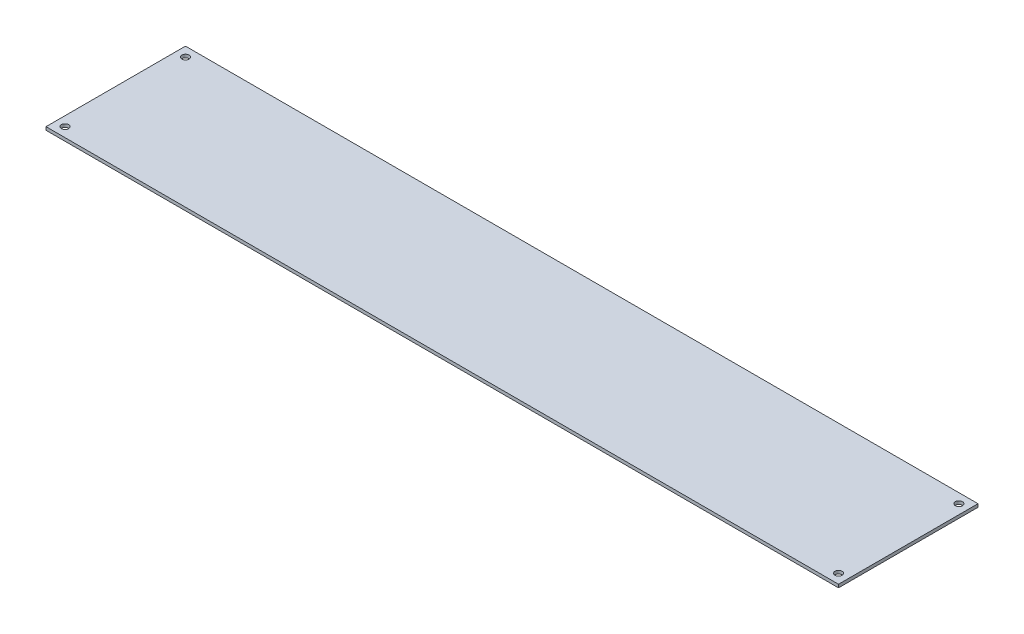
SolidWorks part; units mm, degrees
ref_plane "Front Plane" through (0, 0, 0) normal (0, 0, 1) x (1, 0, 0)
ref_plane "Top Plane" through (0, 0, 0) normal (0, 1, 0) x (1, 0, 0)
ref_plane "Right Plane" through (0, 0, 0) normal (1, 0, 0) x (0, 0, -1)
sketch "Sketch1" plane through (0, 0, 0) normal (0, 1, 0) x (1, 0, 0)
  line L1 (0, 0) -> (500, 0)
  line L2 (0, 0) -> (0, 88)
  line L3 (0, 88) -> (500, 88)
  line L4 (500, 0) -> (500, 88)
  dimension "D1" = 500
  dimension "D2" = 88
extrude "Boss-Extrude1" add sketch "Sketch1" along normal blind 2
hole_wizard "M4 Clearance Hole1" positions "Sketch2" profile "Sketch3" hole size "M4" standard "DIN" end condition up to next
sketch "Sketch2" plane through (0, 2, 0) normal (0, 1, 0) x (1, 0, 0)
  line L0 (500, 88) -> (0, 88) construction
  line L1 (0, 88) -> (0, 0) construction
  line L2 (0, 0) -> (500, 0) construction
  line L3 (500, 0) -> (500, 88) construction
  point P0 (6, 82)
  point P2 (6, 6)
  point P4 (494, 6)
  point P6 (494, 82)
  dimension "D1" = 6
  dimension "D2" = 6
  dimension "D3" = 6
  dimension "D4" = 6
sketch "Sketch3" plane through (6, 2, -82) normal (1, 0, 0) x (0, 0, 1)
  line L0 (0, 0) -> (0, 2)
  line L1 (0, 2) -> (2.25, 2)
  line L2 (2.25, 2) -> (2.25, 0)
  line L5 (2.25, 0) -> (0, 0)
  line L11 (0, -6.35) -> (0, 107.95) construction
  dimension "Thru Hole Dia." = 4.5
  dimension "Thru Hole Depth" = 2
sketch "Sketch4" plane through (0, 2, 0) normal (0, 1, 0) x (1, 0, 0)
  line L0 (500, 0) -> (500, 88) construction
  line L1 (0, 0) -> (500, 0) construction
  line L3 (369.3868, 83) -> (367.9434, 85.5)
  line L4 (367.9434, 85.5) -> (365.0566, 85.5)
  line L5 (365.0566, 85.5) -> (363.6132, 83)
  line L6 (363.6132, 83) -> (365.0566, 80.5)
  line L7 (365.0566, 80.5) -> (367.9434, 80.5)
  line L8 (367.9434, 80.5) -> (369.3868, 83)
  line L9 (379.3868, 83) -> (377.9434, 85.5)
  line L10 (377.9434, 85.5) -> (375.0566, 85.5)
  line L11 (375.0566, 85.5) -> (373.6132, 83)
  line L12 (373.6132, 83) -> (375.0566, 80.5)
  line L13 (375.0566, 80.5) -> (377.9434, 80.5)
  line L14 (377.9434, 80.5) -> (379.3868, 83)
  line L15 (389.3868, 83) -> (387.9434, 85.5)
  line L16 (387.9434, 85.5) -> (385.0566, 85.5)
  line L17 (385.0566, 85.5) -> (383.6132, 83)
  line L18 (383.6132, 83) -> (385.0566, 80.5)
  line L19 (385.0566, 80.5) -> (387.9434, 80.5)
  line L20 (387.9434, 80.5) -> (389.3868, 83)
  line L21 (399.3868, 83) -> (397.9434, 85.5)
  line L22 (397.9434, 85.5) -> (395.0566, 85.5)
  line L23 (395.0566, 85.5) -> (393.6132, 83)
  line L24 (393.6132, 83) -> (395.0566, 80.5)
  line L25 (395.0566, 80.5) -> (397.9434, 80.5)
  line L26 (397.9434, 80.5) -> (399.3868, 83)
  line L27 (409.3868, 83) -> (407.9434, 85.5)
  line L28 (407.9434, 85.5) -> (405.0566, 85.5)
  line L29 (405.0566, 85.5) -> (403.6132, 83)
  line L30 (403.6132, 83) -> (405.0566, 80.5)
  line L31 (405.0566, 80.5) -> (407.9434, 80.5)
  line L32 (407.9434, 80.5) -> (409.3868, 83)
  line L33 (419.3868, 83) -> (417.9434, 85.5)
  line L34 (417.9434, 85.5) -> (415.0566, 85.5)
  line L35 (415.0566, 85.5) -> (413.6132, 83)
  line L36 (413.6132, 83) -> (415.0566, 80.5)
  line L37 (415.0566, 80.5) -> (417.9434, 80.5)
  line L38 (417.9434, 80.5) -> (419.3868, 83)
  line L39 (429.3868, 83) -> (427.9434, 85.5)
  line L40 (427.9434, 85.5) -> (425.0566, 85.5)
  line L41 (425.0566, 85.5) -> (423.6132, 83)
  line L42 (423.6132, 83) -> (425.0566, 80.5)
  line L43 (425.0566, 80.5) -> (427.9434, 80.5)
  line L44 (427.9434, 80.5) -> (429.3868, 83)
  line L45 (439.3868, 83) -> (437.9434, 85.5)
  line L46 (437.9434, 85.5) -> (435.0566, 85.5)
  line L47 (435.0566, 85.5) -> (433.6132, 83)
  line L48 (433.6132, 83) -> (435.0566, 80.5)
  line L49 (435.0566, 80.5) -> (437.9434, 80.5)
  line L50 (437.9434, 80.5) -> (439.3868, 83)
  line L51 (449.3868, 83) -> (447.9434, 85.5)
  line L52 (447.9434, 85.5) -> (445.0566, 85.5)
  line L53 (445.0566, 85.5) -> (443.6132, 83)
  line L54 (443.6132, 83) -> (445.0566, 80.5)
  line L55 (445.0566, 80.5) -> (447.9434, 80.5)
  line L56 (447.9434, 80.5) -> (449.3868, 83)
  line L57 (459.3868, 83) -> (457.9434, 85.5)
  line L58 (457.9434, 85.5) -> (455.0566, 85.5)
  line L59 (455.0566, 85.5) -> (453.6132, 83)
  line L60 (453.6132, 83) -> (455.0566, 80.5)
  line L61 (455.0566, 80.5) -> (457.9434, 80.5)
  line L62 (457.9434, 80.5) -> (459.3868, 83)
  line L63 (469.3868, 83) -> (467.9434, 85.5)
  line L64 (467.9434, 85.5) -> (465.0566, 85.5)
  line L65 (465.0566, 85.5) -> (463.6132, 83)
  line L66 (463.6132, 83) -> (465.0566, 80.5)
  line L67 (465.0566, 80.5) -> (467.9434, 80.5)
  line L68 (467.9434, 80.5) -> (469.3868, 83)
  line L69 (379.3868, 73) -> (377.9434, 75.5)
  line L70 (377.9434, 75.5) -> (375.0566, 75.5)
  line L71 (375.0566, 75.5) -> (373.6132, 73)
  line L72 (373.6132, 73) -> (375.0566, 70.5)
  line L73 (375.0566, 70.5) -> (377.9434, 70.5)
  line L74 (377.9434, 70.5) -> (379.3868, 73)
  line L75 (389.3868, 73) -> (387.9434, 75.5)
  line L76 (387.9434, 75.5) -> (385.0566, 75.5)
  line L77 (385.0566, 75.5) -> (383.6132, 73)
  line L78 (383.6132, 73) -> (385.0566, 70.5)
  line L79 (385.0566, 70.5) -> (387.9434, 70.5)
  line L80 (387.9434, 70.5) -> (389.3868, 73)
  line L81 (399.3868, 73) -> (397.9434, 75.5)
  line L82 (397.9434, 75.5) -> (395.0566, 75.5)
  line L83 (395.0566, 75.5) -> (393.6132, 73)
  line L84 (393.6132, 73) -> (395.0566, 70.5)
  line L85 (395.0566, 70.5) -> (397.9434, 70.5)
  line L86 (397.9434, 70.5) -> (399.3868, 73)
  line L87 (409.3868, 73) -> (407.9434, 75.5)
  line L88 (407.9434, 75.5) -> (405.0566, 75.5)
  line L89 (405.0566, 75.5) -> (403.6132, 73)
  line L90 (403.6132, 73) -> (405.0566, 70.5)
  line L91 (405.0566, 70.5) -> (407.9434, 70.5)
  line L92 (407.9434, 70.5) -> (409.3868, 73)
  line L93 (419.3868, 73) -> (417.9434, 75.5)
  line L94 (417.9434, 75.5) -> (415.0566, 75.5)
  line L95 (415.0566, 75.5) -> (413.6132, 73)
  line L96 (413.6132, 73) -> (415.0566, 70.5)
  line L97 (415.0566, 70.5) -> (417.9434, 70.5)
  line L98 (417.9434, 70.5) -> (419.3868, 73)
  line L99 (429.3868, 73) -> (427.9434, 75.5)
  line L100 (427.9434, 75.5) -> (425.0566, 75.5)
  line L101 (425.0566, 75.5) -> (423.6132, 73)
  line L102 (423.6132, 73) -> (425.0566, 70.5)
  line L103 (425.0566, 70.5) -> (427.9434, 70.5)
  line L104 (427.9434, 70.5) -> (429.3868, 73)
  line L105 (439.3868, 73) -> (437.9434, 75.5)
  line L106 (437.9434, 75.5) -> (435.0566, 75.5)
  line L107 (435.0566, 75.5) -> (433.6132, 73)
  line L108 (433.6132, 73) -> (435.0566, 70.5)
  line L109 (435.0566, 70.5) -> (437.9434, 70.5)
  line L110 (437.9434, 70.5) -> (439.3868, 73)
  line L111 (449.3868, 73) -> (447.9434, 75.5)
  line L112 (447.9434, 75.5) -> (445.0566, 75.5)
  line L113 (445.0566, 75.5) -> (443.6132, 73)
  line L114 (443.6132, 73) -> (445.0566, 70.5)
  line L115 (445.0566, 70.5) -> (447.9434, 70.5)
  line L116 (447.9434, 70.5) -> (449.3868, 73)
  line L117 (459.3868, 73) -> (457.9434, 75.5)
  line L118 (457.9434, 75.5) -> (455.0566, 75.5)
  line L119 (455.0566, 75.5) -> (453.6132, 73)
  line L120 (453.6132, 73) -> (455.0566, 70.5)
  line L121 (455.0566, 70.5) -> (457.9434, 70.5)
  line L122 (457.9434, 70.5) -> (459.3868, 73)
  line L135 (389.3868, 63) -> (387.9434, 65.5)
  line L136 (387.9434, 65.5) -> (385.0566, 65.5)
  line L137 (385.0566, 65.5) -> (383.6132, 63)
  line L138 (383.6132, 63) -> (385.0566, 60.5)
  line L139 (385.0566, 60.5) -> (387.9434, 60.5)
  line L140 (387.9434, 60.5) -> (389.3868, 63)
  line L141 (399.3868, 63) -> (397.9434, 65.5)
  line L142 (397.9434, 65.5) -> (395.0566, 65.5)
  line L143 (395.0566, 65.5) -> (393.6132, 63)
  line L144 (393.6132, 63) -> (395.0566, 60.5)
  line L145 (395.0566, 60.5) -> (397.9434, 60.5)
  line L146 (397.9434, 60.5) -> (399.3868, 63)
  line L147 (409.3868, 63) -> (407.9434, 65.5)
  line L148 (407.9434, 65.5) -> (405.0566, 65.5)
  line L149 (405.0566, 65.5) -> (403.6132, 63)
  line L150 (403.6132, 63) -> (405.0566, 60.5)
  line L151 (405.0566, 60.5) -> (407.9434, 60.5)
  line L152 (407.9434, 60.5) -> (409.3868, 63)
  line L153 (419.3868, 63) -> (417.9434, 65.5)
  line L154 (417.9434, 65.5) -> (415.0566, 65.5)
  line L155 (415.0566, 65.5) -> (413.6132, 63)
  line L156 (413.6132, 63) -> (415.0566, 60.5)
  line L157 (415.0566, 60.5) -> (417.9434, 60.5)
  line L158 (417.9434, 60.5) -> (419.3868, 63)
  line L159 (429.3868, 63) -> (427.9434, 65.5)
  line L160 (427.9434, 65.5) -> (425.0566, 65.5)
  line L161 (425.0566, 65.5) -> (423.6132, 63)
  line L162 (423.6132, 63) -> (425.0566, 60.5)
  line L163 (425.0566, 60.5) -> (427.9434, 60.5)
  line L164 (427.9434, 60.5) -> (429.3868, 63)
  line L165 (439.3868, 63) -> (437.9434, 65.5)
  line L166 (437.9434, 65.5) -> (435.0566, 65.5)
  line L167 (435.0566, 65.5) -> (433.6132, 63)
  line L168 (433.6132, 63) -> (435.0566, 60.5)
  line L169 (435.0566, 60.5) -> (437.9434, 60.5)
  line L170 (437.9434, 60.5) -> (439.3868, 63)
  line L171 (449.3868, 63) -> (447.9434, 65.5)
  line L172 (447.9434, 65.5) -> (445.0566, 65.5)
  line L173 (445.0566, 65.5) -> (443.6132, 63)
  line L174 (443.6132, 63) -> (445.0566, 60.5)
  line L175 (445.0566, 60.5) -> (447.9434, 60.5)
  line L176 (447.9434, 60.5) -> (449.3868, 63)
  line L207 (409.3868, 53) -> (407.9434, 55.5)
  line L208 (407.9434, 55.5) -> (405.0566, 55.5)
  line L209 (405.0566, 55.5) -> (403.6132, 53)
  line L210 (403.6132, 53) -> (405.0566, 50.5)
  line L211 (405.0566, 50.5) -> (407.9434, 50.5)
  line L212 (407.9434, 50.5) -> (409.3868, 53)
  line L213 (419.3868, 53) -> (417.9434, 55.5)
  line L214 (417.9434, 55.5) -> (415.0566, 55.5)
  line L215 (415.0566, 55.5) -> (413.6132, 53)
  line L216 (413.6132, 53) -> (415.0566, 50.5)
  line L217 (415.0566, 50.5) -> (417.9434, 50.5)
  line L218 (417.9434, 50.5) -> (419.3868, 53)
  line L219 (429.3868, 53) -> (427.9434, 55.5)
  line L220 (427.9434, 55.5) -> (425.0566, 55.5)
  line L221 (425.0566, 55.5) -> (423.6132, 53)
  line L222 (423.6132, 53) -> (425.0566, 50.5)
  line L223 (425.0566, 50.5) -> (427.9434, 50.5)
  line L224 (427.9434, 50.5) -> (429.3868, 53)
  line L267 (369.3868, 73) -> (367.9434, 75.5) [skipped]
  line L268 (367.9434, 75.5) -> (365.0566, 75.5) [skipped]
  line L269 (365.0566, 75.5) -> (363.6132, 73) [skipped]
  line L270 (363.6132, 73) -> (365.0566, 70.5) [skipped]
  line L271 (365.0566, 70.5) -> (367.9434, 70.5) [skipped]
  line L272 (367.9434, 70.5) -> (369.3868, 73) [skipped]
  line L273 (369.3868, 63) -> (367.9434, 65.5) [skipped]
  line L274 (367.9434, 65.5) -> (365.0566, 65.5) [skipped]
  line L275 (365.0566, 65.5) -> (363.6132, 63) [skipped]
  line L276 (363.6132, 63) -> (365.0566, 60.5) [skipped]
  line L277 (365.0566, 60.5) -> (367.9434, 60.5) [skipped]
  line L278 (367.9434, 60.5) -> (369.3868, 63) [skipped]
  line L279 (369.3868, 53) -> (367.9434, 55.5) [skipped]
  line L280 (367.9434, 55.5) -> (365.0566, 55.5) [skipped]
  line L281 (365.0566, 55.5) -> (363.6132, 53) [skipped]
  line L282 (363.6132, 53) -> (365.0566, 50.5) [skipped]
  line L283 (365.0566, 50.5) -> (367.9434, 50.5) [skipped]
  line L284 (367.9434, 50.5) -> (369.3868, 53) [skipped]
  line L285 (379.3868, 53) -> (377.9434, 55.5) [skipped]
  line L286 (377.9434, 55.5) -> (375.0566, 55.5) [skipped]
  line L287 (375.0566, 55.5) -> (373.6132, 53) [skipped]
  line L288 (373.6132, 53) -> (375.0566, 50.5) [skipped]
  line L289 (375.0566, 50.5) -> (377.9434, 50.5) [skipped]
  line L290 (377.9434, 50.5) -> (379.3868, 53) [skipped]
  line L291 (379.3868, 63) -> (377.9434, 65.5) [skipped]
  line L292 (377.9434, 65.5) -> (375.0566, 65.5) [skipped]
  line L293 (375.0566, 65.5) -> (373.6132, 63) [skipped]
  line L294 (373.6132, 63) -> (375.0566, 60.5) [skipped]
  line L295 (375.0566, 60.5) -> (377.9434, 60.5) [skipped]
  line L296 (377.9434, 60.5) -> (379.3868, 63) [skipped]
  line L297 (389.3868, 53) -> (387.9434, 55.5) [skipped]
  line L298 (387.9434, 55.5) -> (385.0566, 55.5) [skipped]
  line L299 (385.0566, 55.5) -> (383.6132, 53) [skipped]
  line L300 (383.6132, 53) -> (385.0566, 50.5) [skipped]
  line L301 (385.0566, 50.5) -> (387.9434, 50.5) [skipped]
  line L302 (387.9434, 50.5) -> (389.3868, 53) [skipped]
  line L303 (399.3868, 53) -> (397.9434, 55.5) [skipped]
  line L304 (397.9434, 55.5) -> (395.0566, 55.5) [skipped]
  line L305 (395.0566, 55.5) -> (393.6132, 53) [skipped]
  line L306 (393.6132, 53) -> (395.0566, 50.5) [skipped]
  line L307 (395.0566, 50.5) -> (397.9434, 50.5) [skipped]
  line L308 (397.9434, 50.5) -> (399.3868, 53) [skipped]
  line L309 (439.3868, 53) -> (437.9434, 55.5) [skipped]
  line L310 (437.9434, 55.5) -> (435.0566, 55.5) [skipped]
  line L311 (435.0566, 55.5) -> (433.6132, 53) [skipped]
  line L312 (433.6132, 53) -> (435.0566, 50.5) [skipped]
  line L313 (435.0566, 50.5) -> (437.9434, 50.5) [skipped]
  line L314 (437.9434, 50.5) -> (439.3868, 53) [skipped]
  line L315 (449.3868, 53) -> (447.9434, 55.5) [skipped]
  line L316 (447.9434, 55.5) -> (445.0566, 55.5) [skipped]
  line L317 (445.0566, 55.5) -> (443.6132, 53) [skipped]
  line L318 (443.6132, 53) -> (445.0566, 50.5) [skipped]
  line L319 (445.0566, 50.5) -> (447.9434, 50.5) [skipped]
  line L320 (447.9434, 50.5) -> (449.3868, 53) [skipped]
  line L321 (459.3868, 63) -> (457.9434, 65.5) [skipped]
  line L322 (457.9434, 65.5) -> (455.0566, 65.5) [skipped]
  line L323 (455.0566, 65.5) -> (453.6132, 63) [skipped]
  line L324 (453.6132, 63) -> (455.0566, 60.5) [skipped]
  line L325 (455.0566, 60.5) -> (457.9434, 60.5) [skipped]
  line L326 (457.9434, 60.5) -> (459.3868, 63) [skipped]
  line L327 (459.3868, 53) -> (457.9434, 55.5) [skipped]
  line L328 (457.9434, 55.5) -> (455.0566, 55.5) [skipped]
  line L329 (455.0566, 55.5) -> (453.6132, 53) [skipped]
  line L330 (453.6132, 53) -> (455.0566, 50.5) [skipped]
  line L331 (455.0566, 50.5) -> (457.9434, 50.5) [skipped]
  line L332 (457.9434, 50.5) -> (459.3868, 53) [skipped]
  line L333 (469.3868, 53) -> (467.9434, 55.5) [skipped]
  line L334 (467.9434, 55.5) -> (465.0566, 55.5) [skipped]
  line L335 (465.0566, 55.5) -> (463.6132, 53) [skipped]
  line L336 (463.6132, 53) -> (465.0566, 50.5) [skipped]
  line L337 (465.0566, 50.5) -> (467.9434, 50.5) [skipped]
  line L338 (467.9434, 50.5) -> (469.3868, 53) [skipped]
  line L339 (469.3868, 63) -> (467.9434, 65.5) [skipped]
  line L340 (467.9434, 65.5) -> (465.0566, 65.5) [skipped]
  line L341 (465.0566, 65.5) -> (463.6132, 63) [skipped]
  line L342 (463.6132, 63) -> (465.0566, 60.5) [skipped]
  line L343 (465.0566, 60.5) -> (467.9434, 60.5) [skipped]
  line L344 (467.9434, 60.5) -> (469.3868, 63) [skipped]
  line L345 (469.3868, 73) -> (467.9434, 75.5) [skipped]
  line L346 (467.9434, 75.5) -> (465.0566, 75.5) [skipped]
  line L347 (465.0566, 75.5) -> (463.6132, 73) [skipped]
  line L348 (463.6132, 73) -> (465.0566, 70.5) [skipped]
  line L349 (465.0566, 70.5) -> (467.9434, 70.5) [skipped]
  line L350 (467.9434, 70.5) -> (469.3868, 73) [skipped]
  line L351 (500, 88) -> (0, 88) construction
  circle A0 centre (416.5, 113) radius 66 construction
  circle A1 centre (366.5, 83) radius 2.5 construction
  dimension "D1" = 132
  dimension "D2" = 83.5
  dimension "D3" = 113
  dimension "D4" = 5
  dimension "D5" = 50
  dimension "D6" = 5
  dimension "D9" = 10
  dimension "D10" = 10
  dimension "D7" = 11
  dimension "D8" = 4
extrude "Cut-Extrude1" [suppressed] cut sketch "Sketch4" against normal up to next
sketch "Sketch5" [suppressed] plane through (0, 2, 0) normal (0, 1, 0) x (1, 0, 0)
  line L217 (384.3868, 78) -> (382.9434, 80.5)
  line L218 (374.3868, 78) -> (372.9434, 80.5)
  line L219 (372.9434, 80.5) -> (370.0566, 80.5)
  line L220 (370.0566, 80.5) -> (368.6132, 78)
  line L221 (368.6132, 78) -> (370.0566, 75.5)
  line L222 (370.0566, 75.5) -> (372.9434, 75.5)
  line L223 (372.9434, 75.5) -> (374.3868, 78)
  line L224 (382.9434, 80.5) -> (380.0566, 80.5)
  line L225 (380.0566, 80.5) -> (378.6132, 78)
  line L226 (378.6132, 78) -> (380.0566, 75.5)
  line L227 (380.0566, 75.5) -> (382.9434, 75.5)
  line L228 (382.9434, 75.5) -> (384.3868, 78)
  line L229 (394.3868, 78) -> (392.9434, 80.5)
  line L230 (392.9434, 80.5) -> (390.0566, 80.5)
  line L231 (390.0566, 80.5) -> (388.6132, 78)
  line L232 (388.6132, 78) -> (390.0566, 75.5)
  line L233 (390.0566, 75.5) -> (392.9434, 75.5)
  line L234 (392.9434, 75.5) -> (394.3868, 78)
  line L235 (404.3868, 78) -> (402.9434, 80.5)
  line L236 (402.9434, 80.5) -> (400.0566, 80.5)
  line L237 (400.0566, 80.5) -> (398.6132, 78)
  line L238 (398.6132, 78) -> (400.0566, 75.5)
  line L239 (400.0566, 75.5) -> (402.9434, 75.5)
  line L240 (402.9434, 75.5) -> (404.3868, 78)
  line L241 (414.3868, 78) -> (412.9434, 80.5)
  line L242 (412.9434, 80.5) -> (410.0566, 80.5)
  line L243 (410.0566, 80.5) -> (408.6132, 78)
  line L244 (408.6132, 78) -> (410.0566, 75.5)
  line L245 (410.0566, 75.5) -> (412.9434, 75.5)
  line L246 (412.9434, 75.5) -> (414.3868, 78)
  line L247 (424.3868, 78) -> (422.9434, 80.5)
  line L248 (422.9434, 80.5) -> (420.0566, 80.5)
  line L249 (420.0566, 80.5) -> (418.6132, 78)
  line L250 (418.6132, 78) -> (420.0566, 75.5)
  line L251 (420.0566, 75.5) -> (422.9434, 75.5)
  line L252 (422.9434, 75.5) -> (424.3868, 78)
  line L253 (434.3868, 78) -> (432.9434, 80.5)
  line L254 (432.9434, 80.5) -> (430.0566, 80.5)
  line L255 (430.0566, 80.5) -> (428.6132, 78)
  line L256 (428.6132, 78) -> (430.0566, 75.5)
  line L257 (430.0566, 75.5) -> (432.9434, 75.5)
  line L258 (432.9434, 75.5) -> (434.3868, 78)
  line L259 (444.3868, 78) -> (442.9434, 80.5)
  line L260 (442.9434, 80.5) -> (440.0566, 80.5)
  line L261 (440.0566, 80.5) -> (438.6132, 78)
  line L262 (438.6132, 78) -> (440.0566, 75.5)
  line L263 (440.0566, 75.5) -> (442.9434, 75.5)
  line L264 (442.9434, 75.5) -> (444.3868, 78)
  line L265 (454.3868, 78) -> (452.9434, 80.5)
  line L266 (452.9434, 80.5) -> (450.0566, 80.5)
  line L267 (450.0566, 80.5) -> (448.6132, 78)
  line L268 (448.6132, 78) -> (450.0566, 75.5)
  line L269 (450.0566, 75.5) -> (452.9434, 75.5)
  line L270 (452.9434, 75.5) -> (454.3868, 78)
  line L271 (464.3868, 78) -> (462.9434, 80.5)
  line L272 (462.9434, 80.5) -> (460.0566, 80.5)
  line L273 (460.0566, 80.5) -> (458.6132, 78)
  line L274 (458.6132, 78) -> (460.0566, 75.5)
  line L275 (460.0566, 75.5) -> (462.9434, 75.5)
  line L276 (462.9434, 75.5) -> (464.3868, 78)
  line L277 (384.3868, 68) -> (382.9434, 70.5)
  line L278 (382.9434, 70.5) -> (380.0566, 70.5)
  line L279 (380.0566, 70.5) -> (378.6132, 68)
  line L280 (378.6132, 68) -> (380.0566, 65.5)
  line L281 (380.0566, 65.5) -> (382.9434, 65.5)
  line L282 (382.9434, 65.5) -> (384.3868, 68)
  line L283 (394.3868, 68) -> (392.9434, 70.5)
  line L284 (392.9434, 70.5) -> (390.0566, 70.5)
  line L285 (390.0566, 70.5) -> (388.6132, 68)
  line L286 (388.6132, 68) -> (390.0566, 65.5)
  line L287 (390.0566, 65.5) -> (392.9434, 65.5)
  line L288 (392.9434, 65.5) -> (394.3868, 68)
  line L289 (404.3868, 68) -> (402.9434, 70.5)
  line L290 (402.9434, 70.5) -> (400.0566, 70.5)
  line L291 (400.0566, 70.5) -> (398.6132, 68)
  line L292 (398.6132, 68) -> (400.0566, 65.5)
  line L293 (400.0566, 65.5) -> (402.9434, 65.5)
  line L294 (402.9434, 65.5) -> (404.3868, 68)
  line L295 (414.3868, 68) -> (412.9434, 70.5)
  line L296 (412.9434, 70.5) -> (410.0566, 70.5)
  line L297 (410.0566, 70.5) -> (408.6132, 68)
  line L298 (408.6132, 68) -> (410.0566, 65.5)
  line L299 (410.0566, 65.5) -> (412.9434, 65.5)
  line L300 (412.9434, 65.5) -> (414.3868, 68)
  line L301 (424.3868, 68) -> (422.9434, 70.5)
  line L302 (422.9434, 70.5) -> (420.0566, 70.5)
  line L303 (420.0566, 70.5) -> (418.6132, 68)
  line L304 (418.6132, 68) -> (420.0566, 65.5)
  line L305 (420.0566, 65.5) -> (422.9434, 65.5)
  line L306 (422.9434, 65.5) -> (424.3868, 68)
  line L307 (434.3868, 68) -> (432.9434, 70.5)
  line L308 (432.9434, 70.5) -> (430.0566, 70.5)
  line L309 (430.0566, 70.5) -> (428.6132, 68)
  line L310 (428.6132, 68) -> (430.0566, 65.5)
  line L311 (430.0566, 65.5) -> (432.9434, 65.5)
  line L312 (432.9434, 65.5) -> (434.3868, 68)
  line L313 (444.3868, 68) -> (442.9434, 70.5)
  line L314 (442.9434, 70.5) -> (440.0566, 70.5)
  line L315 (440.0566, 70.5) -> (438.6132, 68)
  line L316 (438.6132, 68) -> (440.0566, 65.5)
  line L317 (440.0566, 65.5) -> (442.9434, 65.5)
  line L318 (442.9434, 65.5) -> (444.3868, 68)
  line L319 (454.3868, 68) -> (452.9434, 70.5)
  line L320 (452.9434, 70.5) -> (450.0566, 70.5)
  line L321 (450.0566, 70.5) -> (448.6132, 68)
  line L322 (448.6132, 68) -> (450.0566, 65.5)
  line L323 (450.0566, 65.5) -> (452.9434, 65.5)
  line L324 (452.9434, 65.5) -> (454.3868, 68)
  line L325 (464.3868, 68) -> (462.9434, 70.5)
  line L326 (462.9434, 70.5) -> (460.0566, 70.5)
  line L327 (460.0566, 70.5) -> (458.6132, 68)
  line L328 (458.6132, 68) -> (460.0566, 65.5)
  line L329 (460.0566, 65.5) -> (462.9434, 65.5)
  line L330 (462.9434, 65.5) -> (464.3868, 68)
  line L337 (394.3868, 58) -> (392.9434, 60.5)
  line L338 (392.9434, 60.5) -> (390.0566, 60.5)
  line L339 (390.0566, 60.5) -> (388.6132, 58)
  line L340 (388.6132, 58) -> (390.0566, 55.5)
  line L341 (390.0566, 55.5) -> (392.9434, 55.5)
  line L342 (392.9434, 55.5) -> (394.3868, 58)
  line L343 (404.3868, 58) -> (402.9434, 60.5)
  line L344 (402.9434, 60.5) -> (400.0566, 60.5)
  line L345 (400.0566, 60.5) -> (398.6132, 58)
  line L346 (398.6132, 58) -> (400.0566, 55.5)
  line L347 (400.0566, 55.5) -> (402.9434, 55.5)
  line L348 (402.9434, 55.5) -> (404.3868, 58)
  line L349 (414.3868, 58) -> (412.9434, 60.5)
  line L350 (412.9434, 60.5) -> (410.0566, 60.5)
  line L351 (410.0566, 60.5) -> (408.6132, 58)
  line L352 (408.6132, 58) -> (410.0566, 55.5)
  line L353 (410.0566, 55.5) -> (412.9434, 55.5)
  line L354 (412.9434, 55.5) -> (414.3868, 58)
  line L355 (424.3868, 58) -> (422.9434, 60.5)
  line L356 (422.9434, 60.5) -> (420.0566, 60.5)
  line L357 (420.0566, 60.5) -> (418.6132, 58)
  line L358 (418.6132, 58) -> (420.0566, 55.5)
  line L359 (420.0566, 55.5) -> (422.9434, 55.5)
  line L360 (422.9434, 55.5) -> (424.3868, 58)
  line L361 (434.3868, 58) -> (432.9434, 60.5)
  line L362 (432.9434, 60.5) -> (430.0566, 60.5)
  line L363 (430.0566, 60.5) -> (428.6132, 58)
  line L364 (428.6132, 58) -> (430.0566, 55.5)
  line L365 (430.0566, 55.5) -> (432.9434, 55.5)
  line L366 (432.9434, 55.5) -> (434.3868, 58)
  line L367 (444.3868, 58) -> (442.9434, 60.5)
  line L368 (442.9434, 60.5) -> (440.0566, 60.5)
  line L369 (440.0566, 60.5) -> (438.6132, 58)
  line L370 (438.6132, 58) -> (440.0566, 55.5)
  line L371 (440.0566, 55.5) -> (442.9434, 55.5)
  line L372 (442.9434, 55.5) -> (444.3868, 58)
  line L403 (414.3868, 48) -> (412.9434, 50.5)
  line L404 (412.9434, 50.5) -> (410.0566, 50.5)
  line L405 (410.0566, 50.5) -> (408.6132, 48)
  line L406 (408.6132, 48) -> (410.0566, 45.5)
  line L407 (410.0566, 45.5) -> (412.9434, 45.5)
  line L408 (412.9434, 45.5) -> (414.3868, 48)
  line L409 (424.3868, 48) -> (422.9434, 50.5)
  line L410 (422.9434, 50.5) -> (420.0566, 50.5)
  line L411 (420.0566, 50.5) -> (418.6132, 48)
  line L412 (418.6132, 48) -> (420.0566, 45.5)
  line L413 (420.0566, 45.5) -> (422.9434, 45.5)
  line L414 (422.9434, 45.5) -> (424.3868, 48)
  line L439 (374.3868, 68) -> (372.9434, 70.5)
  line L440 (372.9434, 70.5) -> (370.0566, 70.5)
  line L441 (370.0566, 70.5) -> (368.6132, 68)
  line L442 (368.6132, 68) -> (370.0566, 65.5)
  line L443 (370.0566, 65.5) -> (372.9434, 65.5)
  line L444 (372.9434, 65.5) -> (374.3868, 68)
  line L457 (374.3868, 58) -> (372.9434, 60.5) [skipped]
  line L458 (372.9434, 60.5) -> (370.0566, 60.5) [skipped]
  line L459 (370.0566, 60.5) -> (368.6132, 58) [skipped]
  line L460 (368.6132, 58) -> (370.0566, 55.5) [skipped]
  line L461 (370.0566, 55.5) -> (372.9434, 55.5) [skipped]
  line L462 (372.9434, 55.5) -> (374.3868, 58) [skipped]
  line L463 (374.3868, 48) -> (372.9434, 50.5) [skipped]
  line L464 (372.9434, 50.5) -> (370.0566, 50.5) [skipped]
  line L465 (370.0566, 50.5) -> (368.6132, 48) [skipped]
  line L466 (368.6132, 48) -> (370.0566, 45.5) [skipped]
  line L467 (370.0566, 45.5) -> (372.9434, 45.5) [skipped]
  line L468 (372.9434, 45.5) -> (374.3868, 48) [skipped]
  line L469 (384.3868, 48) -> (382.9434, 50.5) [skipped]
  line L470 (382.9434, 50.5) -> (380.0566, 50.5) [skipped]
  line L471 (380.0566, 50.5) -> (378.6132, 48) [skipped]
  line L472 (378.6132, 48) -> (380.0566, 45.5) [skipped]
  line L473 (380.0566, 45.5) -> (382.9434, 45.5) [skipped]
  line L474 (382.9434, 45.5) -> (384.3868, 48) [skipped]
  line L475 (384.3868, 58) -> (382.9434, 60.5) [skipped]
  line L476 (382.9434, 60.5) -> (380.0566, 60.5) [skipped]
  line L477 (380.0566, 60.5) -> (378.6132, 58) [skipped]
  line L478 (378.6132, 58) -> (380.0566, 55.5) [skipped]
  line L479 (380.0566, 55.5) -> (382.9434, 55.5) [skipped]
  line L480 (382.9434, 55.5) -> (384.3868, 58) [skipped]
  line L481 (394.3868, 48) -> (392.9434, 50.5) [skipped]
  line L482 (392.9434, 50.5) -> (390.0566, 50.5) [skipped]
  line L483 (390.0566, 50.5) -> (388.6132, 48) [skipped]
  line L484 (388.6132, 48) -> (390.0566, 45.5) [skipped]
  line L485 (390.0566, 45.5) -> (392.9434, 45.5) [skipped]
  line L486 (392.9434, 45.5) -> (394.3868, 48) [skipped]
  line L487 (404.3868, 48) -> (402.9434, 50.5) [skipped]
  line L488 (402.9434, 50.5) -> (400.0566, 50.5) [skipped]
  line L489 (400.0566, 50.5) -> (398.6132, 48) [skipped]
  line L490 (398.6132, 48) -> (400.0566, 45.5) [skipped]
  line L491 (400.0566, 45.5) -> (402.9434, 45.5) [skipped]
  line L492 (402.9434, 45.5) -> (404.3868, 48) [skipped]
  line L493 (434.3868, 48) -> (432.9434, 50.5) [skipped]
  line L494 (432.9434, 50.5) -> (430.0566, 50.5) [skipped]
  line L495 (430.0566, 50.5) -> (428.6132, 48) [skipped]
  line L496 (428.6132, 48) -> (430.0566, 45.5) [skipped]
  line L497 (430.0566, 45.5) -> (432.9434, 45.5) [skipped]
  line L498 (432.9434, 45.5) -> (434.3868, 48) [skipped]
  line L499 (444.3868, 48) -> (442.9434, 50.5) [skipped]
  line L500 (442.9434, 50.5) -> (440.0566, 50.5) [skipped]
  line L501 (440.0566, 50.5) -> (438.6132, 48) [skipped]
  line L502 (438.6132, 48) -> (440.0566, 45.5) [skipped]
  line L503 (440.0566, 45.5) -> (442.9434, 45.5) [skipped]
  line L504 (442.9434, 45.5) -> (444.3868, 48) [skipped]
  line L505 (454.3868, 48) -> (452.9434, 50.5) [skipped]
  line L506 (452.9434, 50.5) -> (450.0566, 50.5) [skipped]
  line L507 (450.0566, 50.5) -> (448.6132, 48) [skipped]
  line L508 (448.6132, 48) -> (450.0566, 45.5) [skipped]
  line L509 (450.0566, 45.5) -> (452.9434, 45.5) [skipped]
  line L510 (452.9434, 45.5) -> (454.3868, 48) [skipped]
  line L511 (454.3868, 58) -> (452.9434, 60.5) [skipped]
  line L512 (452.9434, 60.5) -> (450.0566, 60.5) [skipped]
  line L513 (450.0566, 60.5) -> (448.6132, 58) [skipped]
  line L514 (448.6132, 58) -> (450.0566, 55.5) [skipped]
  line L515 (450.0566, 55.5) -> (452.9434, 55.5) [skipped]
  line L516 (452.9434, 55.5) -> (454.3868, 58) [skipped]
  line L517 (464.3868, 58) -> (462.9434, 60.5) [skipped]
  line L518 (462.9434, 60.5) -> (460.0566, 60.5) [skipped]
  line L519 (460.0566, 60.5) -> (458.6132, 58) [skipped]
  line L520 (458.6132, 58) -> (460.0566, 55.5) [skipped]
  line L521 (460.0566, 55.5) -> (462.9434, 55.5) [skipped]
  line L522 (462.9434, 55.5) -> (464.3868, 58) [skipped]
  line L523 (464.3868, 48) -> (462.9434, 50.5) [skipped]
  line L524 (462.9434, 50.5) -> (460.0566, 50.5) [skipped]
  line L525 (460.0566, 50.5) -> (458.6132, 48) [skipped]
  line L526 (458.6132, 48) -> (460.0566, 45.5) [skipped]
  line L527 (460.0566, 45.5) -> (462.9434, 45.5) [skipped]
  line L528 (462.9434, 45.5) -> (464.3868, 48) [skipped]
  circle A0 centre (371.5, 78) radius 2.5 construction
  circle A2 centre (366.5, 83) radius 2.5 construction
  dimension "D3" = 10
  dimension "D1" = 5
  dimension "D2" = 5
  dimension "D5" = 10
  dimension "D6" = 10
  dimension "D4" = 4
extrude "Cut-Extrude2" [suppressed] cut sketch "Sketch5" against normal up to next
